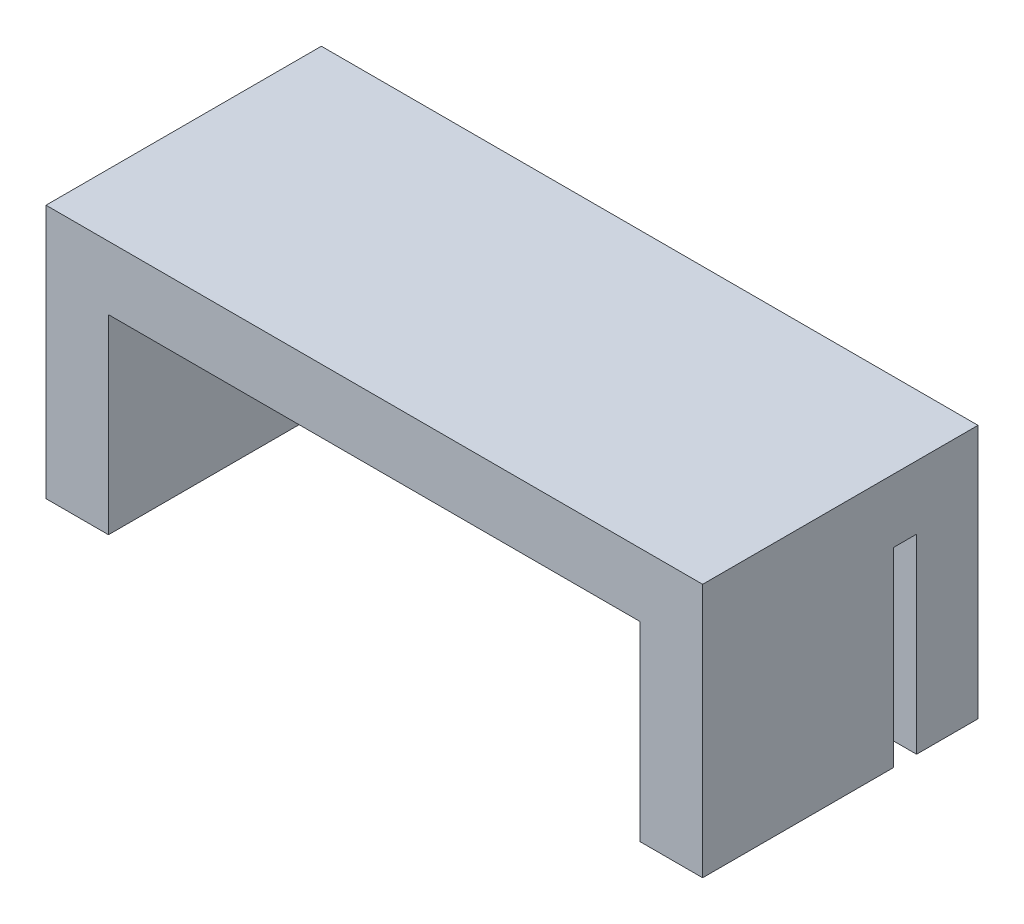
SolidWorks part; units mm, degrees
ref_plane "Alzado" through (0, 0, 0) normal (0, 0, 1) x (1, 0, 0)
ref_plane "Planta" through (0, 0, 0) normal (0, 1, 0) x (1, 0, 0)
ref_plane "Vista lateral" through (0, 0, 0) normal (1, 0, 0) x (0, 0, -1)
sketch "Croquis2" plane through (0, 0, 0) normal (0, 0, 1) x (1, 0, 0)
  line L1 (-15.5, -6) -> (15.5, -6)
  line L2 (-15.5, -6) -> (-15.5, 6)
  line L3 (-15.5, 6) -> (15.5, 6)
  line L4 (15.5, -6) -> (15.5, 6)
  line L5 (-15.5, -6) -> (15.5, 6) construction
  line L6 (-15.5, 6) -> (15.5, -6) construction
  point P0 (0, 0)
  dimension "D1" = 31
  dimension "D2" = 12
extrude "Saliente-Extruir1" add sketch "Croquis2" along normal blind 13
sketch "Croquis3" plane through (0, -6, 0) normal (0, -1, 0) x (1, 0, 0)
  line L0 (-15.5, 13) -> (15.5, 13) construction
  line L1 (-12.55, 13) -> (12.55, 13)
  line L2 (-12.55, 13) -> (-12.55, 2.9)
  line L3 (-12.55, 2.9) -> (12.55, 2.9)
  line L4 (12.55, 13) -> (12.55, 2.9)
  line L7 (-15.5, 0) -> (15.5, 0) construction
  line L8 (0, 2.9) -> (0, 0) construction
  dimension "D1" = 25.1
  dimension "D2" = 2.9
extrude "Cortar-Extruir1" cut sketch "Croquis3" against normal blind 9
sketch "Croquis6" plane through (-15.5, 0, 0) normal (-1, 0, 0) x (0, 0, 1)
  line L0 (13, -6) -> (0, -6) construction
  line L1 (4, -6) -> (2.9, -6)
  line L2 (4, -6) -> (4, 3)
  line L3 (4, 3) -> (2.9, 3)
  line L4 (2.9, -6) -> (2.9, 3)
  line L5 (0, 6) -> (0, -6) construction
  line L6 (13, 6) -> (0, 6) construction
  dimension "D1" = 2.9
  dimension "D2" = 1.1
  dimension "D3" = 3
extrude "Cortar-Extruir3" cut sketch "Croquis6" against normal through all
sketch "Croquis7" plane through (0, 0, 0) normal (0, 0, -1) x (-1, 0, 0)
  circle A0 centre (-8.4125, -2.05) radius 1.5
  circle A1 centre (8.4125, -2.05) radius 1.5
  circle A2 centre (-8.4125, -2.05) radius 2.8 construction
  circle A3 centre (8.4125, -2.05) radius 2.8 construction
  dimension "D1" = 3
extrude "Cortar-Extruir4" cut sketch "Croquis7" against normal through all
